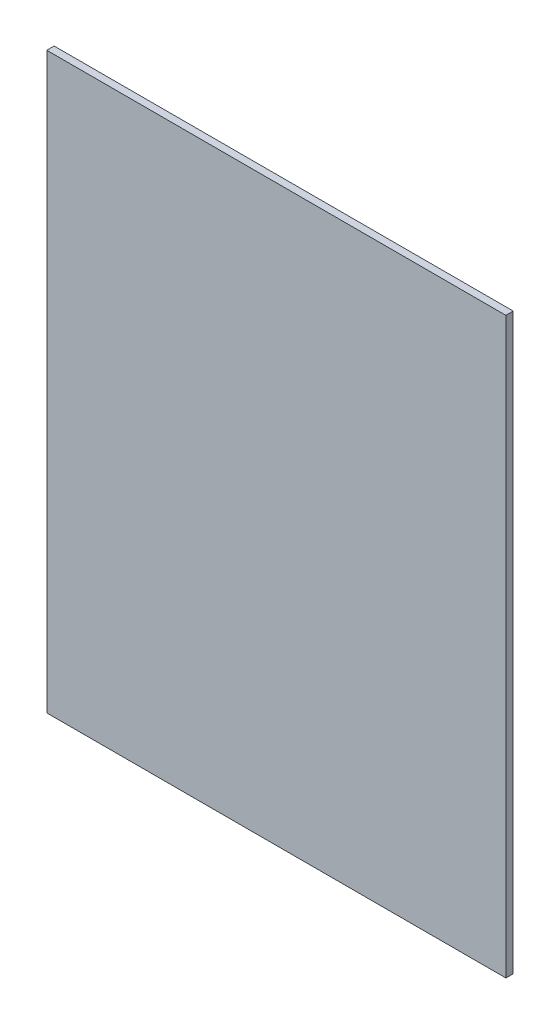
SolidWorks part; units mm, degrees
ref_plane "Front Plane" through (0, 0, 0) normal (0, 0, 1) x (1, 0, 0)
ref_plane "Top Plane" through (0, 0, 0) normal (0, 1, 0) x (1, 0, 0)
ref_plane "Right Plane" through (0, 0, 0) normal (1, 0, 0) x (0, 0, -1)
sketch "Sketch1" plane through (0, 0, 0) normal (0, 0, 1) x (1, 0, 0)
  line L1 (-99.06, -123.825) -> (99.06, -123.825)
  line L2 (-99.06, -123.825) -> (-99.06, 123.825)
  line L3 (-99.06, 123.825) -> (99.06, 123.825)
  line L4 (99.06, -123.825) -> (99.06, 123.825)
  line L5 (-99.06, -123.825) -> (99.06, 123.825) construction
  line L6 (-99.06, 123.825) -> (99.06, -123.825) construction
  point P0 (0, 0)
  dimension "D1" = 198.12
  dimension "D2" = 247.65
extrude "Boss-Extrude1" add sketch "Sketch1" along normal blind 3.175
